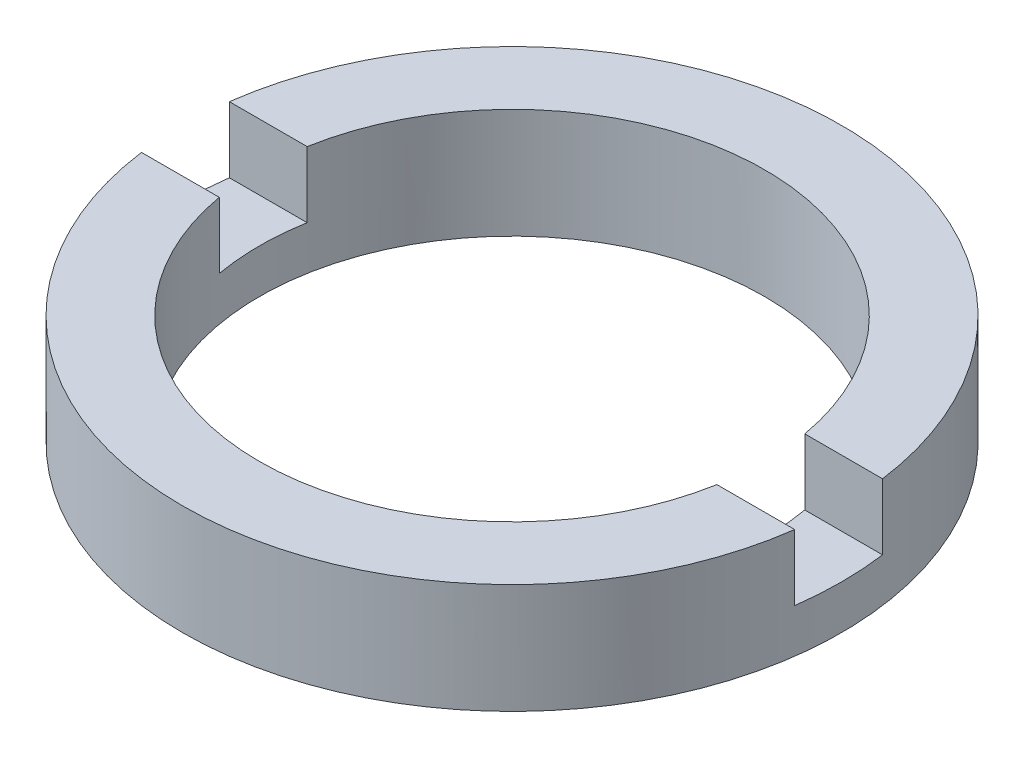
SolidWorks part; units mm, degrees
ref_plane "前视基准面" through (0, 0, 0) normal (0, 0, 1) x (1, 0, 0)
ref_plane "上视基准面" through (0, 0, 0) normal (0, 1, 0) x (1, 0, 0)
ref_plane "右视基准面" through (0, 0, 0) normal (1, 0, 0) x (0, 0, -1)
sketch "草图1" plane through (0, 0, 0) normal (0, 0, 1) x (1, 0, 0)
  line L0 (0, 56.2608) -> (0, -99.1922) construction
  line L1 (5.75, -1.9642) -> (7.5, -1.9642)
  line L4 (7.5, -1.9642) -> (7.5, -4.4642)
  line L5 (5.75, -4.4642) -> (5.75, -1.9642)
  line L7 (5.75, -4.4642) -> (7.5, -4.4642)
  dimension "D1" = 2.5
  dimension "D2" = 7.5
  dimension "D3" = 5.75
revolve "旋转1" add sketch "草图1" angle 360 about L0
cosmetic thread "装饰螺纹线1" parameters "D2"=14
sketch "草图2" plane through (0, -1.9642, 0) normal (0, 1, 0) x (1, 0, 0)
  line L0 (-28.67, 0) -> (29.9422, 0) construction
  line L2 (-26.8525, 1) -> (26.8525, 1)
  line L3 (-26.8525, 1) -> (-26.8525, -1)
  line L4 (-26.8525, -1) -> (26.8525, -1)
  line L5 (26.8525, 1) -> (26.8525, -1)
  line L6 (-26.8525, 1) -> (26.8525, -1) construction
  line L7 (-26.8525, -1) -> (26.8525, 1) construction
  point P3 (0, 0)
  dimension "D1" = 2
extrude "切除-拉伸1" cut sketch "草图2" against normal blind 1.5
